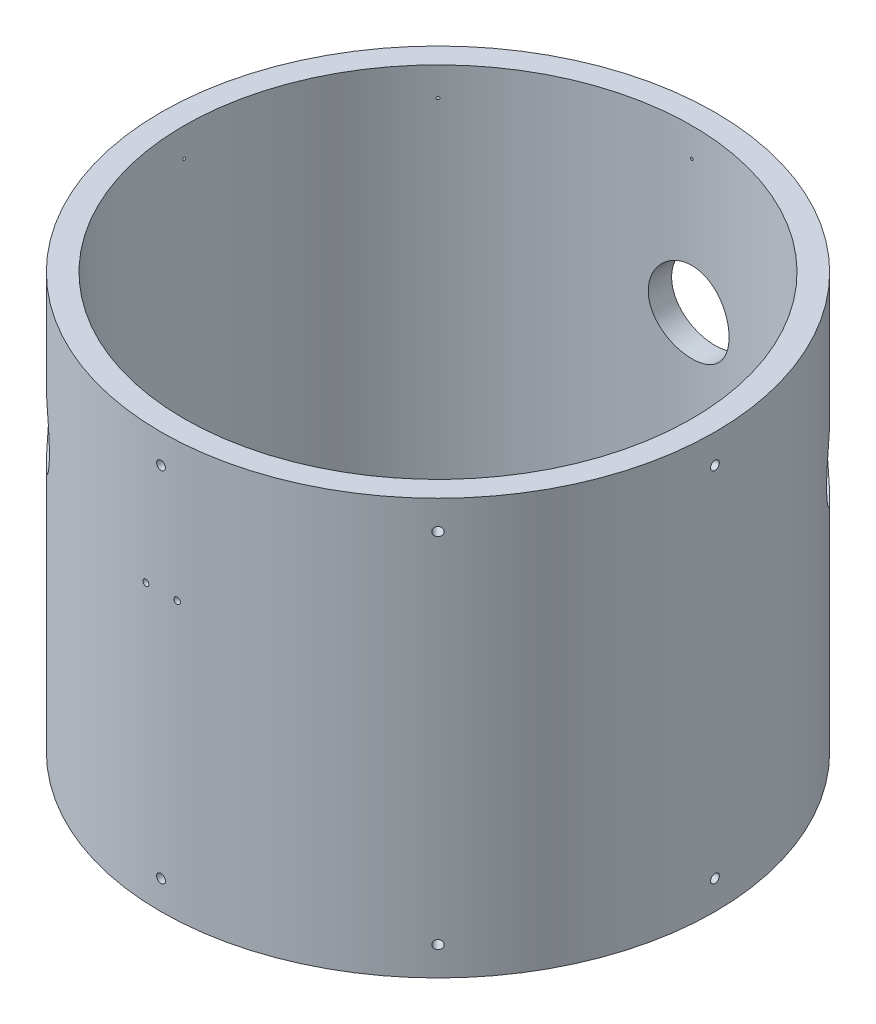
SolidWorks part; units mm, degrees
ref_plane "Front Plane" through (0, 0, 0) normal (0, 0, 1) x (1, 0, 0)
ref_plane "Top Plane" through (0, 0, 0) normal (0, 1, 0) x (1, 0, 0)
ref_plane "Right Plane" through (0, 0, 0) normal (1, 0, 0) x (0, 0, -1)
sketch "Sketch1" plane through (0, 0, 0) normal (0, 1, 0) x (1, 0, 0)
  circle A0 centre (0, 0) radius 152.4
  circle A1 centre (0, 0) radius 139.7
  dimension "D1" = 304.8
  dimension "D2" = 279.4
extrude "Boss-Extrude1" add sketch "Sketch1" along normal blind 228.6
ref_plane "Plane1" through (0, 0, 152.4) normal (0, 0, 1) x (1, 0, 0)
hole_wizard "#10-32 Tapped Hole1" positions "Sketch2" profile "Sketch3" tap size "#10-32" standard "ANSI Inch"
sketch "Sketch2" plane through (0, 0, 152.4) normal (0, 0, 1) x (1, 0, 0)
  line L0 (-152.4, 0) -> (152.4, 0) construction
  line L1 (152.4, 228.6) -> (-152.4, 228.6) construction
  line L2 (0, 212.725) -> (0, 15.875)
  line L3 (0, 15.875) -> (0, 0)
  point P0 (0, 212.725)
  point P2 (0, 15.875)
  dimension "D1" = 15.875
  dimension "D2" = 15.875
sketch "Sketch3" plane through (0, 212.725, 152.4) normal (1, 0, 0) x (0, -1, 0)
  line L0 (0, 0) -> (0, 13.1513)
  line L1 (0, 13.1513) -> (2.0193, 11.938)
  line L2 (2.0193, 11.938) -> (2.0193, 9.652)
  line L3 (2.0193, 9.652) -> (2.413, 9.652)
  line L4 (2.413, 9.652) -> (2.413, 0)
  line L5 (2.413, 0) -> (0, 0)
  line L10 (0, 13.1513) -> (-2.0193, 11.938) construction
  line L11 (0, -6.35) -> (0, 107.95) construction
  dimension "Tap Drill Dia." = 4.0386
  dimension "Tap Drill Depth" = 11.938
  dimension "Thread Major Dia." = 4.826
  dimension "Thread Depth" = 9.652
  dimension "Drill Angle" = 118
pattern_circular "CirPattern1" count 8 over 360 about axis through (0, 0, 0) along (0, 1, 0) of "#10-32 Tapped Hole1"
hole_wizard "#8-32 Tapped Hole1" positions "Sketch4" profile "Sketch5" tap size "#8-32" standard "ANSI Inch"
sketch "Sketch4" plane through (0, 0, 152.4) normal (0, 0, 1) x (1, 0, 0)
  line L1 (-8.5725, 152.4) -> (8.5725, 152.4)
  line L3 (0, 152.4) -> (0, 0)
  point P0 (-8.5725, 152.4)
  point P2 (8.5725, 152.4)
  dimension "D1" = 17.145
  dimension "D2" = 152.4
sketch "Sketch5" plane through (-8.5725, 152.4, 152.4) normal (1, 0, 0) x (0, -1, 0)
  line L0 (0, 0) -> (0, 11.7058)
  line L1 (0, 11.7058) -> (1.7272, 10.668)
  line L2 (1.7272, 10.668) -> (1.7272, 0)
  line L5 (1.7272, 0) -> (0, 0)
  line L10 (0, 11.7058) -> (-1.7272, 10.668) construction
  line L11 (0, -6.35) -> (0, 107.95) construction
  dimension "Tap Drill Dia." = 3.4544
  dimension "Tap Drill Depth" = 10.668
  dimension "Drill Angle" = 118
cosmetic thread "Hole Thread1" parameters "D1"=8.382, "D2"=4.1656
cosmetic thread "Hole Thread2" parameters "D1"=8.382, "D2"=4.1656
ref_plane "Plane2" through (-107.7631, 0, 107.7631) normal (-0.7071, 0, 0.7071) x (0, -1, 0)
ref_plane "Plane3" through (107.7631, 0, -107.7631) normal (0.7071, 0, -0.7071) x (-0.7071, 0, -0.7071)
hole_wizard "Pressure Relif Hole" positions "Sketch10" profile "Sketch11" legacy
sketch "Sketch10" plane through (107.7631, 0, -107.7631) normal (0.7071, 0, -0.7071) x (-0.7071, 0, -0.7071)
  line L0 (-152.4, 0) -> (152.4, 0) construction
  line L1 (0, 139.7) -> (0, 0)
  point P0 (0, 139.7)
  dimension "D1" = 139.7
sketch "Sketch11" plane through (107.7631, 139.7, -107.7631) normal (0, 1, 0) x (-0.7071, 0, -0.7071)
  line L0 (0, 0) -> (0, 12.7)
  line L1 (0, 12.7) -> (19.05, 12.7)
  line L2 (19.05, 12.7) -> (19.05, 0)
  line L3 (19.05, 0) -> (0, 0)
  line L4 (0, 110) -> (0, -10) construction
  dimension "Diameter" = 38.1
  dimension "Depth" = 12.7
hole_wizard "Vent Valve Hole" positions "Sketch7" profile "Sketch9" legacy
sketch "Sketch7" plane through (-107.7631, 0, 107.7631) normal (-0.7071, 0, 0.7071) x (0, -1, 0)
  line L0 (-155.575, 0) -> (-212.725, 0)
  line L2 (0, -152.4) -> (0, 152.4) construction
  point P0 (-155.575, 0)
  dimension "D1" = 155.575
sketch "Sketch9" plane through (-107.7631, 155.575, 107.7631) normal (0, 1, 0) x (0.7071, 0, 0.7071)
  line L0 (0, 0) -> (0, 25.4)
  line L1 (0, 25.4) -> (19.05, 25.4)
  line L2 (19.05, 25.4) -> (19.05, 0)
  line L3 (19.05, 0) -> (0, 0)
  line L4 (0, 110) -> (0, -10) construction
  dimension "Diameter" = 38.1
  dimension "Depth" = 25.4
ref_plane "Plane4" through (0, 0, -152.4) normal (0, 0, -1) x (0, -1, 0)
hole_wizard "Helium In" positions "Sketch14" profile "Sketch15" legacy
sketch "Sketch14" plane through (0, 0, -152.4) normal (0, 0, -1) x (0, -1, 0)
  line L0 (0, -152.4) -> (0, 152.4) construction
  point P0 (-139.7, 0)
  dimension "D1" = 139.7
sketch "Sketch15" plane through (0, 139.7, -152.4) normal (1, 0, 0) x (0, 1, 0)
  line L0 (0, 0) -> (0, 12.7)
  line L1 (0, 12.7) -> (22.225, 12.7)
  line L2 (22.225, 12.7) -> (22.225, 0)
  line L3 (22.225, 0) -> (0, 0)
  line L4 (0, 110) -> (0, -10) construction
  dimension "Diameter" = 44.45
  dimension "Depth" = 12.7
